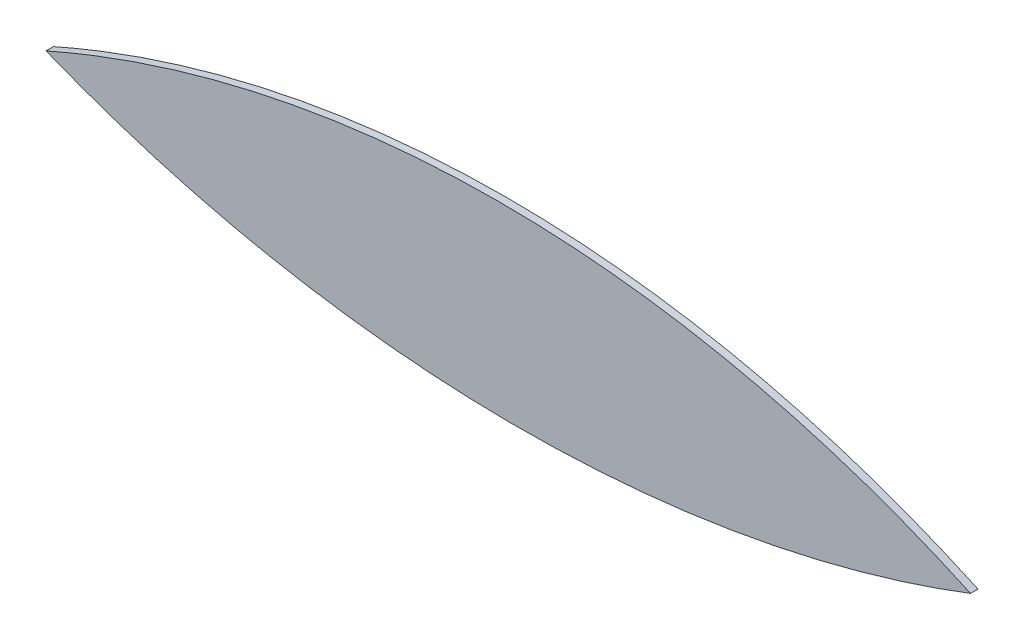
SolidWorks part; units mm, degrees
ref_plane "Alzado" through (0, 0, 0) normal (0, 0, 1) x (1, 0, 0)
ref_plane "Planta" through (0, 0, 0) normal (0, 1, 0) x (1, 0, 0)
ref_plane "Vista lateral" through (0, 0, 0) normal (1, 0, 0) x (0, 0, -1)
sketch "Model" plane through (0, 0, 0) normal (0, 0, 1) x (1, 0, 0)
  spline S0 degree 2 poles (59.0077, 26.8579) (52.845, 29.7069) (46.6364, 26.9595) knots 0.914488 0.914488 0.914488 1.76414 1.76414 1.76414 weights 1 0.91111 1
  spline S1 degree 2 poles (46.6364, 26.9595) (52.7908, 24.4739) (59.0077, 26.8579) knots 0 0 0 0.914488 0.914488 0.914488 weights 1 0.897273 1
extrude "Saliente-Extruir1" add sketch "Model" along normal blind 0.1
